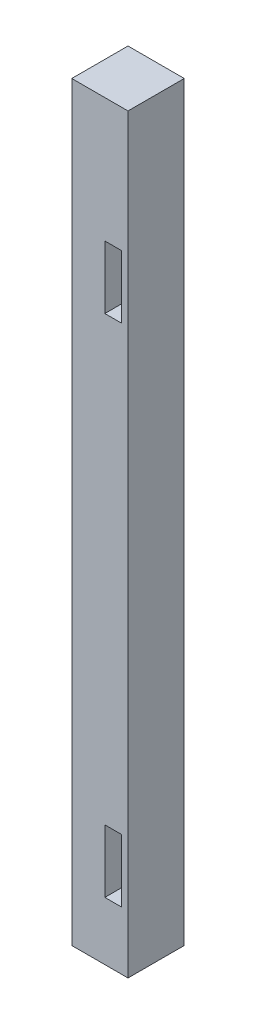
SolidWorks part; units mm, degrees
ref_plane "Front" through (0, 0, 0) normal (0, 0, 1) x (1, 0, 0)
ref_plane "Top" through (0, 0, 0) normal (0, 1, 0) x (1, 0, 0)
ref_plane "Right" through (0, 0, 0) normal (1, 0, 0) x (0, 0, -1)
sketch "Sketch1" plane through (0, 0, 0) normal (0, 1, 0) x (1, 0, 0)
  line L1 (-4.25, 4.25) -> (4.25, 4.25)
  line L2 (-4.25, 4.25) -> (-4.25, -4.25)
  line L3 (-4.25, -4.25) -> (4.25, -4.25)
  line L4 (4.25, 4.25) -> (4.25, -4.25)
  line L5 (-4.25, 4.25) -> (4.25, -4.25) construction
  line L6 (-4.25, -4.25) -> (4.25, 4.25) construction
  point P0 (0, 0)
  dimension "D1" = 8.5
  dimension "D2" = 8.5
extrude "Boss-Extrude1" add sketch "Sketch1" along normal blind 113.5
sketch "Sketch2" plane through (0, 0, 4.25) normal (0, 0, 1) x (1, 0, 0)
  line L1 (3.25, 18.3) -> (0.75, 18.3)
  line L2 (3.25, 18.3) -> (3.25, 8.8)
  line L3 (3.25, 8.8) -> (0.75, 8.8)
  line L4 (0.75, 18.3) -> (0.75, 8.8)
  line L5 (-4.25, 0) -> (4.25, 0) construction
  line L6 (-4.25, 113.5) -> (4.25, 113.5) construction
  line L7 (0.75, 94.73) -> (3.25, 94.73)
  line L8 (0.75, 94.73) -> (0.75, 85.23)
  line L9 (0.75, 85.23) -> (3.25, 85.23)
  line L10 (3.25, 94.73) -> (3.25, 85.23)
  line L11 (4.25, 113.5) -> (4.25, 0) construction
  dimension "D1" = 9.5
  dimension "D2" = 2.5
  dimension "D3" = 1
  dimension "D4" = 8.8
  dimension "D5" = 2.5
  dimension "D6" = 9.5
  dimension "D7" = 18.77
  dimension "D8" = 1
extrude "Cut-Extrude1" cut sketch "Sketch2" against normal blind 5
sketch "Sketch3" plane through (-4.25, 0, 0) normal (-1, 0, 0) x (0, 0, 1)
  line L1 (-3.25, 104.7) -> (-0.75, 104.7)
  line L2 (-3.25, 104.7) -> (-3.25, 95.2)
  line L3 (-3.25, 95.2) -> (-0.75, 95.2)
  line L4 (-0.75, 104.7) -> (-0.75, 95.2)
  line L5 (-4.25, 113.5) -> (4.25, 113.5) construction
  line L6 (-4.25, 0) -> (4.25, 0) construction
  line L7 (-3.25, 28.27) -> (-0.75, 28.27)
  line L8 (-3.25, 28.27) -> (-3.25, 18.77)
  line L9 (-3.25, 18.77) -> (-0.75, 18.77)
  line L10 (-0.75, 28.27) -> (-0.75, 18.77)
  line L11 (-4.25, 113.5) -> (-4.25, 0) construction
  dimension "D1" = 2.5
  dimension "D2" = 9.5
  dimension "D3" = 1
  dimension "D4" = 8.8
  dimension "D5" = 9.5
  dimension "D6" = 18.77
  dimension "D7" = 2.5
  dimension "D8" = 1
extrude "Cut-Extrude2" cut sketch "Sketch3" against normal blind 5
